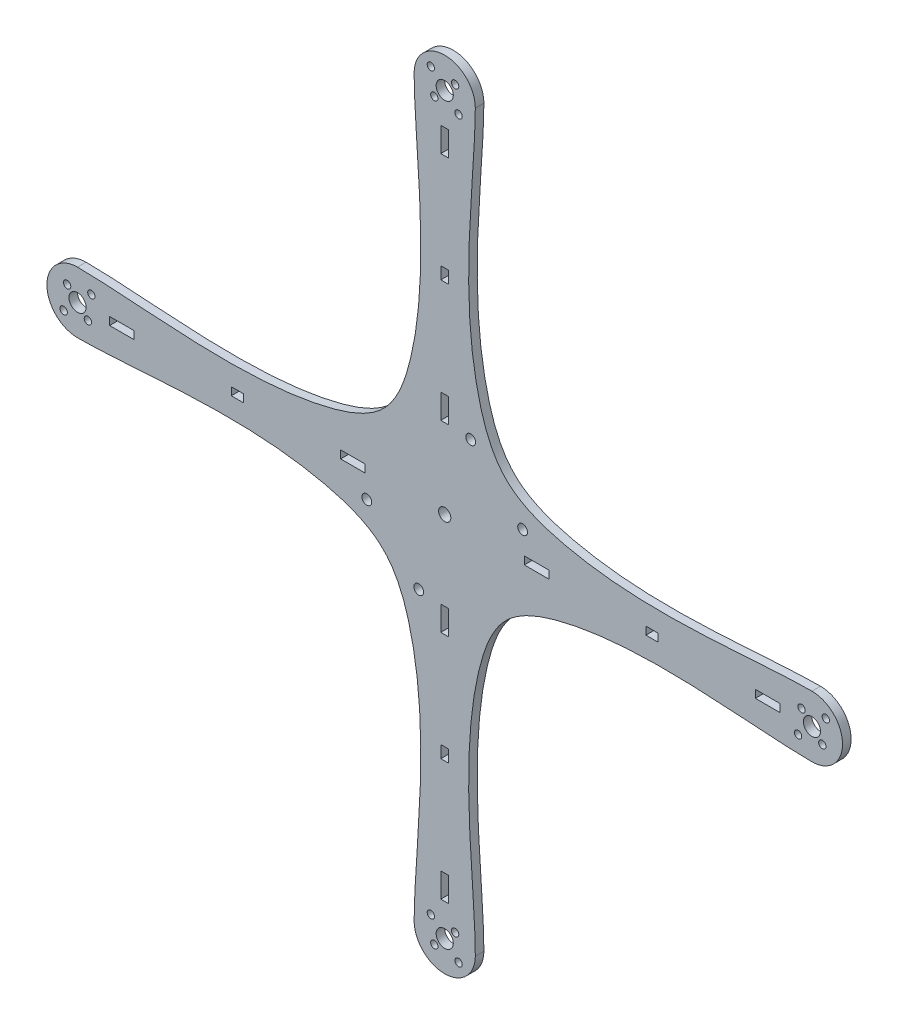
SolidWorks part; units mm, degrees
ref_plane "Front Plane" through (0, 0, 0) normal (0, 0, 1) x (1, 0, 0)
ref_plane "Top Plane" through (0, 0, 0) normal (0, 1, 0) x (1, 0, 0)
ref_plane "Right Plane" through (0, 0, 0) normal (1, 0, 0) x (0, 0, -1)
sketch "Sketch1" plane through (0, 0, 0) normal (0, 0, 1) x (1, 0, 0)
  line L0 (-150, 0) -> (0, 0) construction
  line L1 (0, 0) -> (150, 0) construction
  line L2 (0, 0) -> (0, -150) construction
  line L3 (0, 0) -> (0, 150) construction
  line L4 (50, 0) -> (0, 50) construction
  line L5 (0, 50) -> (-50, 0) construction
  line L6 (-50, 0) -> (0, -50) construction
  line L7 (0, -50) -> (50, 0) construction
  line L8 (1.6, -42.5) -> (-1.6, -42.5)
  line L9 (1.6, -42.5) -> (1.6, -32.5)
  line L10 (-150, -12.5) -> (-130, -12.5) construction
  line L11 (-12.5, -150) -> (-12.5, -140) construction
  line L12 (-144.3431, 5.6569) -> (-155.6569, -5.6569) construction
  line L13 (-154.2426, 4.2426) -> (-145.7574, -4.2426) construction
  line L14 (-136, 0) -> (-101, 0) construction
  line L15 (1.6, -32.5) -> (-1.6, -32.5)
  line L16 (-1.6, -42.5) -> (-1.6, -32.5)
  line L17 (1.6, -42.5) -> (-1.6, -32.5) construction
  line L30 (-136, 0) -> (-50, 0) construction
  line L31 (-42.5, -1.6) -> (-42.5, 1.6)
  line L44 (-42.5, 1.6) -> (-32.5, 1.6)
  line L45 (-32.5, -1.6) -> (-32.5, 1.6)
  line L46 (-42.5, -1.6) -> (-32.5, -1.6)
  line L151 (-37.5, 0) -> (-14, 0) construction
  line L152 (-37.5, 0) -> (-14, 0) construction
  line L158 (-1.6, 42.5) -> (1.6, 42.5)
  line L159 (1.6, 42.5) -> (1.6, 32.5)
  line L171 (-1.6, 32.5) -> (1.6, 32.5)
  line L172 (-1.6, 42.5) -> (-1.6, 32.5)
  line L173 (42.5, 1.6) -> (42.5, -1.6)
  line L174 (10.6066, 31.8198) -> (31.8198, 10.6066) construction
  line L175 (42.5, -1.6) -> (32.5, -1.6)
  line L176 (32.5, 1.6) -> (32.5, -1.6)
  line L177 (42.5, 1.6) -> (32.5, 1.6)
  line L178 (0, -130) -> (0, -37.5) construction
  line L184 (0, -84.6854) -> (-9.8172, -84.6854) construction
  line L186 (1.6, -126.8709) -> (1.6, -136.8709)
  line L187 (1.6, -136.8709) -> (-1.6, -136.8709)
  line L188 (-1.6, -126.8709) -> (-1.6, -136.8709)
  line L189 (1.6, -126.8709) -> (-1.6, -126.8709)
  line L190 (-126.8709, -1.6) -> (-136.8709, -1.6)
  line L191 (-136.8709, -1.6) -> (-136.8709, 1.6)
  line L192 (-126.8709, 1.6) -> (-136.8709, 1.6)
  line L193 (-126.8709, -1.6) -> (-126.8709, 1.6)
  line L194 (-1.6, 126.8709) -> (-1.6, 136.8709)
  line L195 (-1.6, 136.8709) -> (1.6, 136.8709)
  line L196 (1.6, 126.8709) -> (1.6, 136.8709)
  line L197 (-1.6, 126.8709) -> (1.6, 126.8709)
  line L198 (126.8709, 1.6) -> (136.8709, 1.6)
  line L199 (136.8709, 1.6) -> (136.8709, -1.6)
  line L200 (126.8709, -1.6) -> (136.8709, -1.6)
  line L201 (126.8709, 1.6) -> (126.8709, -1.6)
  line L207 (-82.1854, 1.6) -> (-87.1854, 1.6)
  line L208 (-1.6, -82.1854) -> (1.6, -82.1854)
  line L209 (-1.6, -82.1854) -> (-1.6, -87.1854)
  line L210 (-1.6, -87.1854) -> (1.6, -87.1854)
  line L211 (1.6, -82.1854) -> (1.6, -87.1854)
  line L212 (-1.6, -82.1854) -> (1.6, -87.1854) construction
  line L213 (-1.6, -87.1854) -> (1.6, -82.1854) construction
  line L214 (-82.1854, 1.6) -> (-82.1854, -1.6)
  line L215 (-82.1854, -1.6) -> (-87.1854, -1.6)
  line L216 (-87.1854, 1.6) -> (-87.1854, -1.6)
  line L217 (1.6, 82.1854) -> (1.6, 87.1854)
  line L218 (1.6, 82.1854) -> (-1.6, 82.1854)
  line L219 (-1.6, 82.1854) -> (-1.6, 87.1854)
  line L220 (1.6, 87.1854) -> (-1.6, 87.1854)
  line L221 (82.1854, -1.6) -> (87.1854, -1.6)
  line L222 (82.1854, -1.6) -> (82.1854, 1.6)
  line L223 (82.1854, 1.6) -> (87.1854, 1.6)
  line L224 (87.1854, -1.6) -> (87.1854, 1.6)
  line L225 (0, 0) -> (21.2132, 21.2132) construction
  line L226 (0, 0) -> (7.7782, 7.7782)
  line L227 (13.0815, 2.4749) -> (2.4749, 13.0815) construction
  line L228 (2.4749, 13.0815) -> (-13.0815, -2.4749) construction
  line L229 (-13.0815, -2.4749) -> (-2.4749, -13.0815) construction
  line L230 (-2.4749, -13.0815) -> (13.0815, 2.4749) construction
  arc A0 (-12.5, -150) -> (12.5, -150) centre (0, -150) ccw
  arc A1 (-150, 12.5) -> (-150, -12.5) centre (-150, 0) ccw
  arc A2 (12.5, 150) -> (-12.5, 150) centre (0, 150) ccw
  arc A3 (150, -12.5) -> (150, 12.5) centre (150, 0) ccw
  circle A5 centre (-155.6569, -5.6569) radius 1.5
  circle A6 centre (-144.3431, 5.6569) radius 1.5
  circle A7 centre (-145.7574, -4.2426) radius 1.5
  circle A8 centre (-154.2426, 4.2426) radius 1.5
  circle A9 centre (-5.6569, 155.6569) radius 1.5
  circle A10 centre (-4.2426, 145.7574) radius 1.5
  circle A11 centre (5.6569, 144.3431) radius 1.5
  circle A12 centre (4.2426, 154.2426) radius 1.5
  circle A13 centre (155.6569, 5.6569) radius 1.5
  circle A14 centre (145.7574, 4.2426) radius 1.5
  circle A15 centre (144.3431, -5.6569) radius 1.5
  circle A16 centre (154.2426, -4.2426) radius 1.5
  circle A17 centre (5.6569, -155.6569) radius 1.5
  circle A18 centre (4.2426, -145.7574) radius 1.5
  circle A19 centre (-5.6569, -144.3431) radius 1.5
  circle A20 centre (-4.2426, -154.2426) radius 1.5
  circle A25 centre (-150, 0) radius 3.5
  circle A26 centre (0, 150) radius 3.5
  circle A27 centre (150, 0) radius 3.5
  circle A28 centre (0, -150) radius 3.5
  circle A29 centre (0, 0) radius 37.5 construction
  circle A30 centre (0, 0) radius 2.5
  circle A31 centre (10.6066, 31.8198) radius 2
  circle A32 centre (31.8198, 10.6066) radius 2
  circle A33 centre (-10.6066, -31.8198) radius 2
  circle A34 centre (-31.8198, -10.6066) radius 2
  spline S0 degree 3 poles (-12.5, -150) (-12.5, -125.1194) (-3.7089, -72.8468) (-22.3437, -22.345) (-72.8585, -3.7072) (-125.0121, -12.5) (-150, -12.5) knots 0 0 0 0 0.361155 0.451427 0.541698 0.902854 0.902854 0.902854 0.902854
  spline S1 degree 3 poles (-150, 12.5) (-125.1194, 12.5) (-72.8468, 3.7089) (-22.345, 22.3437) (-3.7072, 72.8585) (-12.5, 125.0121) (-12.5, 150) knots 0 0 0 0 0.361155 0.451427 0.541698 0.902854 0.902854 0.902854 0.902854
  spline S2 degree 3 poles (12.5, 150) (12.5, 125.1194) (3.7089, 72.8468) (22.3437, 22.345) (72.8585, 3.7072) (125.0121, 12.5) (150, 12.5) knots 0 0 0 0 0.361155 0.451427 0.541698 0.902854 0.902854 0.902854 0.902854
  spline S3 degree 3 poles (150, -12.5) (125.1194, -12.5) (72.8468, -3.7089) (22.345, -22.3437) (3.7072, -72.8585) (12.5, -125.0121) (12.5, -150) knots 0 0 0 0 0.361155 0.451427 0.541698 0.902854 0.902854 0.902854 0.902854
  point P2 (0, -37.5)
  point P14 (-150, 0)
  point P16 (0, 0)
  point P27 (-150, 0)
  point P46 (0, 0)
  point P77 (0, 0)
  point P78 (0, -37.5)
  point P88 (-118.5, 0)
  point P95 (0, 0)
  point P116 (-93, 0)
  point P118 (0, 0)
  point P138 (0, 0)
  point P141 (7.7782, 7.7782)
  point P221 (0, 0)
  point P228 (0, 0)
  point P229 (-25.75, 0)
  point P249 (0, 0)
  point P254 (21.2132, 21.2132)
  point P448 (0, 0)
  dimension "D2" = 25
  dimension "D3" = 4
  dimension "D4" = 3.2
  dimension "D9" = 3
  dimension "D12" = 10
  dimension "D14" = 7
  dimension "D16" = 75
  dimension "D21" = 5
  dimension "D24" = 15
  dimension "D13" = 0
  dimension "D20" = 4
  dimension "D1" = 300
  dimension "D5" = 20
  dimension "D6" = 10
  dimension "D7" = 16
  dimension "D8" = 12
  dimension "D11" = 35
  dimension "D17" = 4
  dimension "D18" = 5
  dimension "D19" = 3.2
  dimension "D22" = 11
  dimension "D23" = 30
  dimension "D25" = 22
  dimension "D10" = 4
  dimension "D15" = 4
extrude "Boss-Extrude1" add sketch "Sketch1" along normal blind 3.5
